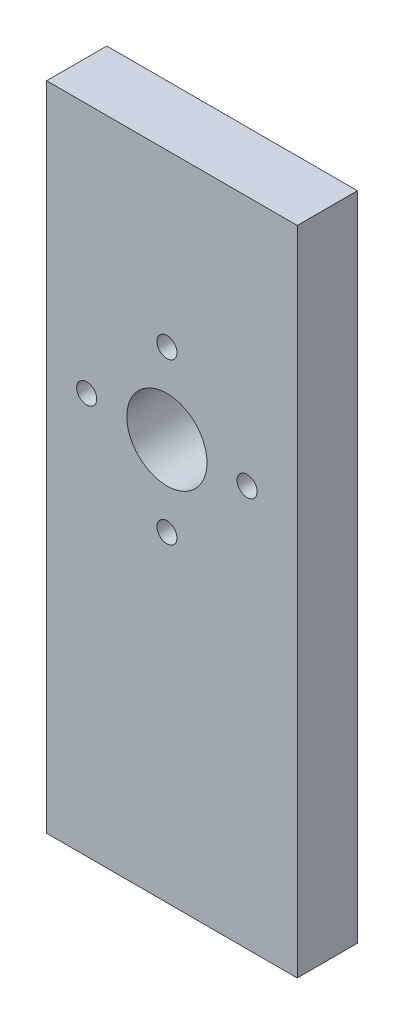
SolidWorks part; units mm, degrees
ref_plane "Plan de face" through (0, 0, 0) normal (0, 0, 1) x (1, 0, 0)
ref_plane "Plan de dessus" through (0, 0, 0) normal (0, 1, 0) x (1, 0, 0)
ref_plane "Plan de droite" through (0, 0, 0) normal (1, 0, 0) x (0, 0, -1)
sketch "Esquisse1" plane through (0, 0, 0) normal (0, 0, 1) x (1, 0, 0)
  line L0 (25.3646, -115.6707) -> (25.3646, -50.6707)
  line L1 (50.3646, -50.6707) -> (25.3646, -50.6707)
  line L2 (50.3646, -50.6707) -> (50.3646, -115.6707)
  line L3 (50.3646, -115.6707) -> (25.3646, -115.6707)
  circle A2 centre (29.3646, -75.6707) radius 1
  circle A3 centre (37.3646, -67.6707) radius 1
  circle A4 centre (45.3646, -75.6707) radius 1
  circle A5 centre (37.3646, -83.6707) radius 1
  circle A7 centre (37.3646, -75.6707) radius 4
  dimension "D3" = 25
  dimension "D11" = 25
  dimension "D10" = 13
  dimension "D6" = 2
  dimension "D7" = 2
  dimension "D8" = 2
  dimension "D9" = 2
  dimension "D4" = 8
  dimension "D1" = 65
  dimension "D2" = 65
  dimension "D5" = 25
extrude "Boss.-Extru.1" add sketch "Esquisse1" along normal blind 6
sketch "Esquisse4" plane through (25.3646, 0, 0) normal (-1, 0, 0) x (0, 0, 1)
  line L0 (6, -50.6707) -> (6, -115.6707) construction
  line L3 (6, -50.6707) -> (0, -50.6707) construction
  line L4 (6, -115.6707) -> (0, -115.6707) construction
  circle A0 centre (3, -55.6707) radius 1.5
  circle A1 centre (3, -110.6707) radius 1.5
  point P6 (3, -50.6707)
  dimension "D1" = 3
  dimension "D2" = 3
  dimension "D3" = 3
  dimension "D4" = 3
  dimension "D5" = 5
  dimension "D6" = 5
extrude "Enlèv. mat.-Extru.3" cut sketch "Esquisse4" against normal blind 10
